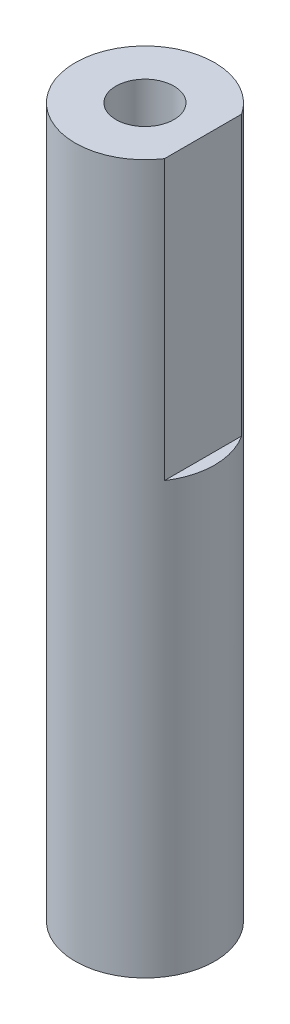
SolidWorks part; units mm, degrees
material "Chrome Stainless Steel"
ref_plane "Front Plane" through (0, 0, 0) normal (0, 0, 1) x (1, 0, 0)
ref_plane "Top Plane" through (0, 0, 0) normal (0, 1, 0) x (1, 0, 0)
ref_plane "Right Plane" through (0, 0, 0) normal (1, 0, 0) x (0, 0, -1)
sketch "Sketch1" plane through (0, 0, 0) normal (0, 1, 0) x (1, 0, 0)
  circle A0 centre (0, 0) radius 3
  dimension "D1" = 6
extrude "SHAFT" add sketch "Sketch1" along normal blind 20.5 and the other way blind 10
sketch "Sketch2" plane through (0, 20.5, 0) normal (0, 1, 0) x (1, 0, 0)
  line L0 (0, 0) -> (2.5, 0) construction
  line L1 (2.5, 3) -> (3, 3)
  line L2 (2.5, 3) -> (2.5, -3)
  line L3 (2.5, -3) -> (3, -3)
  line L4 (3, 3) -> (3, -3)
  line L5 (0, 0) -> (-3, 0) construction
  circle A0 centre (0, 0) radius 3 construction
  point P9 (-3, 0)
  dimension "D1" = 0.5
  dimension "D2" = 6
  dimension "D3" = 5.5
extrude "KEY" cut sketch "Sketch2" against normal blind 12
hole_wizard "M3x0.5 Tapped Hole1" positions "Sketch3" profile "Sketch4" tap size "M3x0.5" standard "ANSI Metric"
sketch "Sketch3" plane through (0, 20.5, 0) normal (0, 1, 0) x (1, 0, 0)
  point P0 (0, 0)
sketch "Sketch4" plane through (0, 20.5, 0) normal (1, 0, 0) x (0, 0, 1)
  line L0 (0, 0) -> (0, 15.2511)
  line L1 (0, 15.2511) -> (1.25, 14.5)
  line L2 (1.25, 14.5) -> (1.25, 0)
  line L5 (1.25, 0) -> (0, 0)
  line L10 (0, 15.2511) -> (-1.25, 14.5) construction
  line L11 (0, -6.35) -> (0, 107.95) construction
  dimension "Tap Drill Dia." = 2.5
  dimension "Tap Drill Depth" = 14.5
  dimension "Drill Angle" = 118
cosmetic thread "Hole Thread1" parameters "D1"=12, "D2"=3
